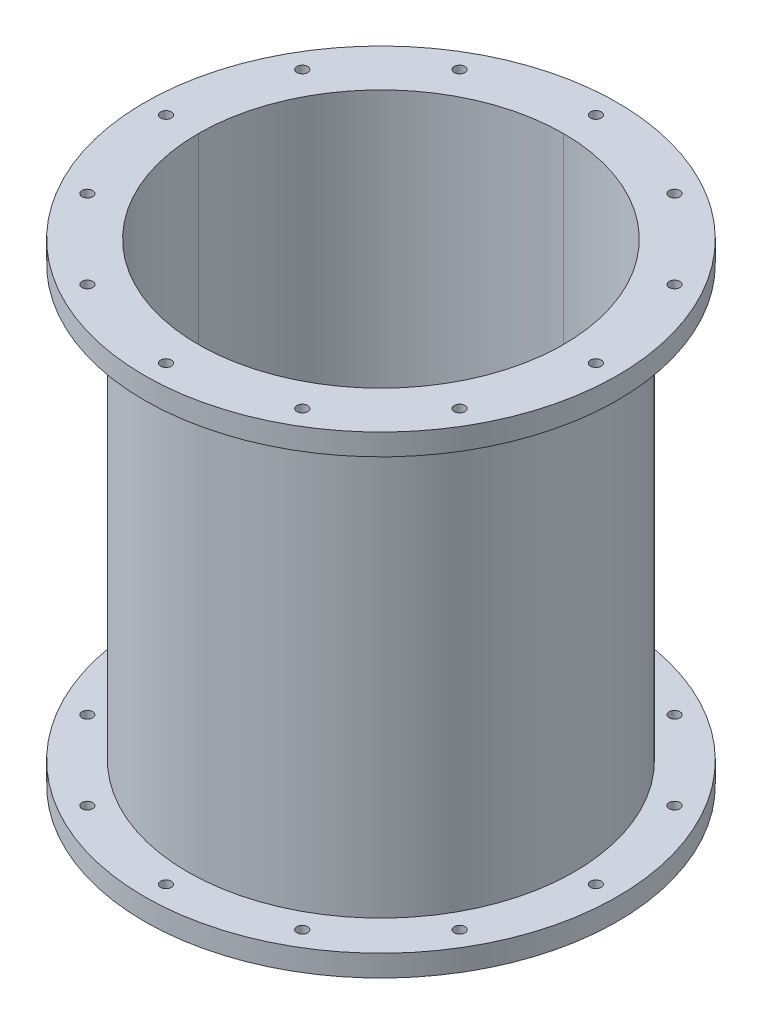
SolidWorks part; units mm, degrees
material "Plain Carbon Steel"
ref_plane "Front Plane" through (0, 0, 0) normal (0, 0, 1) x (1, 0, 0)
ref_plane "Top Plane" through (0, 0, 0) normal (0, 1, 0) x (1, 0, 0)
ref_plane "Right Plane" through (0, 0, 0) normal (1, 0, 0) x (0, 0, -1)
sketch "Sketch1" plane through (0, 0, 0) normal (0, 1, 0) x (1, 0, 0)
  line L0 (0, 139.7) -> (0, -139.7)
  line L1 (-139.7, 0) -> (139.7, 0)
  line L2 (0, 0) -> (0, 127) construction
  circle A0 centre (0, 0) radius 107.95
  circle A1 centre (0, 0) radius 114.3
  circle A2 centre (0, 0) radius 127
  circle A3 centre (0, 0) radius 139.7
  circle A4 centre (0, 127) radius 3.175
  circle A6 centre (127, 0) radius 3.175
  circle A7 centre (0, 0) radius 127
  circle A8 centre (0, 0) radius 127
  circle A9 centre (0, 0) radius 127
  circle A10 centre (0, 0) radius 127
  circle A11 centre (0, 0) radius 127
  circle A12 centre (0, 0) radius 127
  circle A13 centre (0, 0) radius 127
  circle A14 centre (0, 0) radius 127
  circle A15 centre (0, 0) radius 127
  circle A16 centre (0, 0) radius 127
  circle A17 centre (0, 0) radius 127
  circle A18 centre (63.5, 109.9852) radius 3.175
  circle A19 centre (109.9852, 63.5) radius 3.175
  circle A20 centre (127, 0) radius 3.175
  circle A21 centre (109.9852, -63.5) radius 3.175
  circle A22 centre (63.5, -109.9852) radius 3.175
  circle A23 centre (0, -127) radius 3.175
  circle A24 centre (-63.5, -109.9852) radius 3.175
  circle A25 centre (-109.9852, -63.5) radius 3.175
  circle A26 centre (-127, 0) radius 3.175
  circle A27 centre (-109.9852, 63.5) radius 3.175
  circle A28 centre (-63.5, 109.9852) radius 3.175
  point P39 (0, 0)
  dimension "D1" = 215.9
  dimension "D2" = 228.6
  dimension "D3" = 254
  dimension "D4" = 279.4
  dimension "D5" = 6.35
  dimension "D6" = 6.35
  dimension "D7" = 12
  dimension "D8" = 12
extrude "Boss-Extrude1" add sketch "Sketch1" along normal mid plane 279.4 contours L0 A0 L1 | L1 A0 L0 | L1 A0 L0 | L0 A2 L1 A1 | L0 A3 L1 A2 | L0 A1 L1 A0 | L1 A2 L0 A1 | L1 A1 L0 A0 | L1 A3 L0 A2 | L1 A3 L0 A2 | L1 A2 L0 A1 | L1 A1 L0 A0 | L0 A1 L1 A0 | L0 A2 L1 A1 | L0 A3 L1 A2
ref_plane "Plane1" through (0, 0, 0) normal (0, 1, 0) x (1, 0, 0)
sketch "Sketch6" plane through (0, 0, 0) normal (0, 1, 0) x (1, 0, 0)
  arc A0 (0, 107.95) -> (-107.95, 0) centre (0, 0) ccw construction
  arc A1 (-107.95, 0) -> (0, 107.95) centre (0, 0) ccw construction
  arc A2 (0, 107.95) -> (-107.95, 0) centre (0, 0) ccw
  arc A3 (-107.95, 0) -> (0, 107.95) centre (0, 0) ccw
  circle A4 centre (0, 0) radius 114.2863
  circle A5 centre (0, 0) radius 139.7 construction
  circle A6 centre (0, 0) radius 139.7
  circle A7 centre (-109.9852, 63.5) radius 3.175 construction
  circle A8 centre (-127, 0) radius 3.175 construction
  circle A9 centre (-109.9852, -63.5) radius 3.175 construction
  circle A10 centre (-63.5, -109.9852) radius 3.175 construction
  circle A11 centre (0, -127) radius 3.175 construction
  circle A12 centre (63.5, -109.9852) radius 3.175 construction
  circle A13 centre (109.9852, -63.5) radius 3.175 construction
  circle A14 centre (127, 0) radius 3.175 construction
  circle A15 centre (109.9852, 63.5) radius 3.175 construction
  circle A16 centre (63.5, 109.9852) radius 3.175 construction
  circle A17 centre (0, 127) radius 3.175 construction
  circle A18 centre (-63.5, 109.9852) radius 3.175 construction
  circle A19 centre (-109.9852, 63.5) radius 3.175
  circle A20 centre (-127, 0) radius 3.175
  circle A21 centre (-109.9852, -63.5) radius 3.175
  circle A22 centre (-63.5, -109.9852) radius 3.175
  circle A23 centre (0, -127) radius 3.175
  circle A24 centre (63.5, -109.9852) radius 3.175
  circle A25 centre (109.9852, -63.5) radius 3.175
  circle A26 centre (127, 0) radius 3.175
  circle A27 centre (109.9852, 63.5) radius 3.175
  circle A28 centre (63.5, 109.9852) radius 3.175
  circle A29 centre (0, 127) radius 3.175
  circle A30 centre (-63.5, 109.9852) radius 3.175
extrude "Cut-Extrude4" cut sketch "Sketch6" against normal mid plane 254 contours A6 A30 A29 A28 A27 A26 A25 A24 A23 A22 A21 A20 A19 A4
